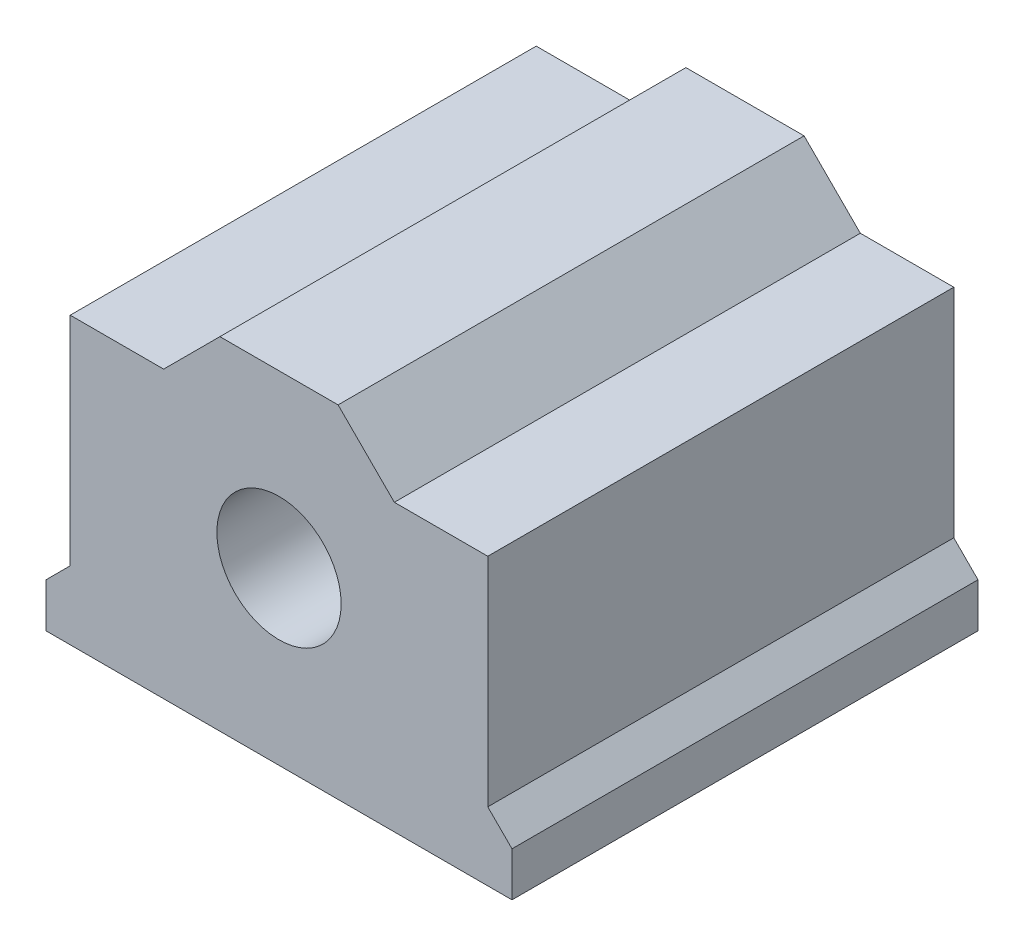
SolidWorks part; units mm, degrees
material "Plain Carbon Steel"
ref_plane "Front Plane" through (0, 0, 0) normal (0, 0, 1) x (1, 0, 0)
ref_plane "Top Plane" through (0, 0, 0) normal (0, 1, 0) x (1, 0, 0)
ref_plane "Right Plane" through (0, 0, 0) normal (1, 0, 0) x (0, 0, -1)
sketch "Sketch1" plane through (0, 0, 0) normal (0, 1, 0) x (1, 0, 0)
  line L1 (0, 0) -> (30, 0)
  line L2 (0, 0) -> (0, 30)
  line L3 (0, 30) -> (30, 30)
  line L4 (30, 0) -> (30, 30)
  dimension "D1" = 30
  dimension "D2" = 30
extrude "Boss-Extrude1" add sketch "Sketch1" along normal blind 22
sketch "Sketch2" plane through (0, 0, 0) normal (0, 0, 1) x (1, 0, 0)
  line L0 (15, 22) -> (15, 0) construction
  line L1 (0, 22) -> (30, 22) construction
  line L2 (0, 0) -> (30, 0) construction
  line L3 (0, 2.8474) -> (1.5596, 4.407)
  line L4 (0, 22) -> (0, 0) construction
  line L5 (1.5596, 4.407) -> (1.5596, 18.3791)
  line L6 (1.5596, 18.3791) -> (7.5745, 18.3791)
  line L7 (7.5745, 18.3791) -> (11.1954, 22)
  line L8 (11.1954, 22) -> (15, 22)
  line L9 (0, 2.8474) -> (0, 0)
  line L10 (22.4255, 18.3791) -> (18.8046, 22)
  line L11 (28.4404, 18.3791) -> (22.4255, 18.3791)
  line L12 (28.4404, 4.407) -> (28.4404, 18.3791)
  line L13 (30, 2.8474) -> (28.4404, 4.407)
  line L14 (30, 2.8474) -> (30, 0)
  line L15 (15, 22) -> (18.8046, 22)
  circle A0 centre (15, 11) radius 4
  line M8 (30, 0) -> (30, 22)
  line M9 (30, 22) -> (0, 22)
  line M10 (0, 22) -> (0, 0)
  dimension "D1" = 8
  dimension "D2" = 11
extrude "Cut-Extrude1" cut sketch "Sketch2" against normal through all contours L6 L7 L3 L5 M9 M10 | L13 L10 L11 L12 M8 M9 | A0 L0 | L0 A0
